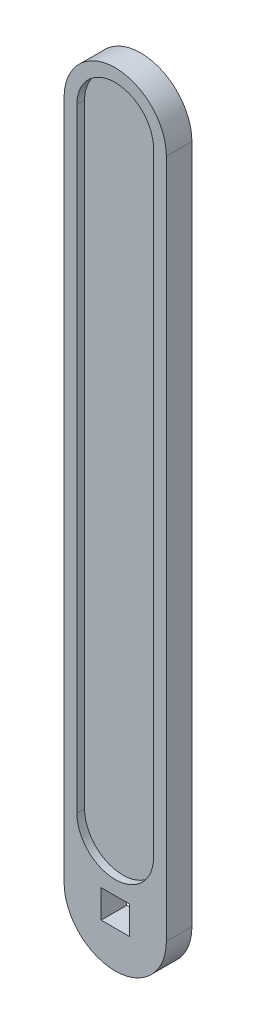
SolidWorks part; units mm, degrees
material "普通碳钢"
ref_plane "前视基准面" through (0, 0, 0) normal (0, 0, 1) x (1, 0, 0)
ref_plane "上视基准面" through (0, 0, 0) normal (0, 1, 0) x (1, 0, 0)
ref_plane "右视基准面" through (0, 0, 0) normal (1, 0, 0) x (0, 0, -1)
sketch "草图1" plane through (0, 0, 0) normal (0, 0, 1) x (1, 0, 0)
  line L0 (0, 0) -> (0, 120) construction
  line L1 (-7.5, 0) -> (-7.5, 120)
  line L2 (7.5, 0) -> (7.5, 120)
  arc A0 (-7.5, 0) -> (7.5, 0) centre (0, 0) ccw
  arc A1 (7.5, 120) -> (-7.5, 120) centre (0, 120) ccw
  point P3 (0, 60)
  dimension "D1" = 120
  dimension "D2" = 15
extrude "凸台-拉伸1" add sketch "草图1" along normal mid plane 2
sketch "草图2" plane through (0, 0, 0) normal (0, 0, 1) x (1, 0, 0)
  line L5 (-10, 0) -> (-10, -13)
  line L6 (10, -13) -> (10, 0)
  line L7 (10, 0) -> (10, 120)
  line L8 (-10, 120) -> (-10, 0)
  line L9 (10, 0) -> (10, 120)
  line L10 (-10, 120) -> (-10, 0)
  line L11 (-7.5, 120) -> (-7.5, 0) construction
  line L12 (2.75, -15.75) -> (-2.75, -15.75)
  line L13 (2.75, -15.75) -> (2.75, -10.25)
  line L14 (2.75, -10.25) -> (-2.75, -10.25)
  line L15 (-2.75, -15.75) -> (-2.75, -10.25)
  line L16 (2.75, -15.75) -> (-2.75, -10.25) construction
  line L17 (2.75, -10.25) -> (-2.75, -15.75) construction
  line L18 (7.5, 0) -> (7.5, 120) construction
  line L19 (-7.5, 120) -> (-7.5, 0)
  line L20 (7.5, 0) -> (7.5, 120)
  arc A3 (-10, -13) -> (10, -13) centre (0, -13) ccw
  arc A4 (10, 120) -> (-10, 120) centre (0, 120) ccw
  arc A5 (10, 120) -> (-10, 120) centre (0, 120) ccw
  arc A6 (7.5, 120) -> (-7.5, 120) centre (0, 120) ccw construction
  arc A7 (-7.5, 0) -> (7.5, 0) centre (0, 0) ccw construction
  arc A8 (7.5, 120) -> (-7.5, 120) centre (0, 120) ccw
  arc A9 (-7.5, 0) -> (7.5, 0) centre (0, 0) ccw
  dimension "D2" = 5.5
  dimension "D3" = 5.5
  dimension "D4" = 13
  dimension "D1" = 2.5
extrude "凸台-拉伸2" add sketch "草图2" along normal mid plane 5
